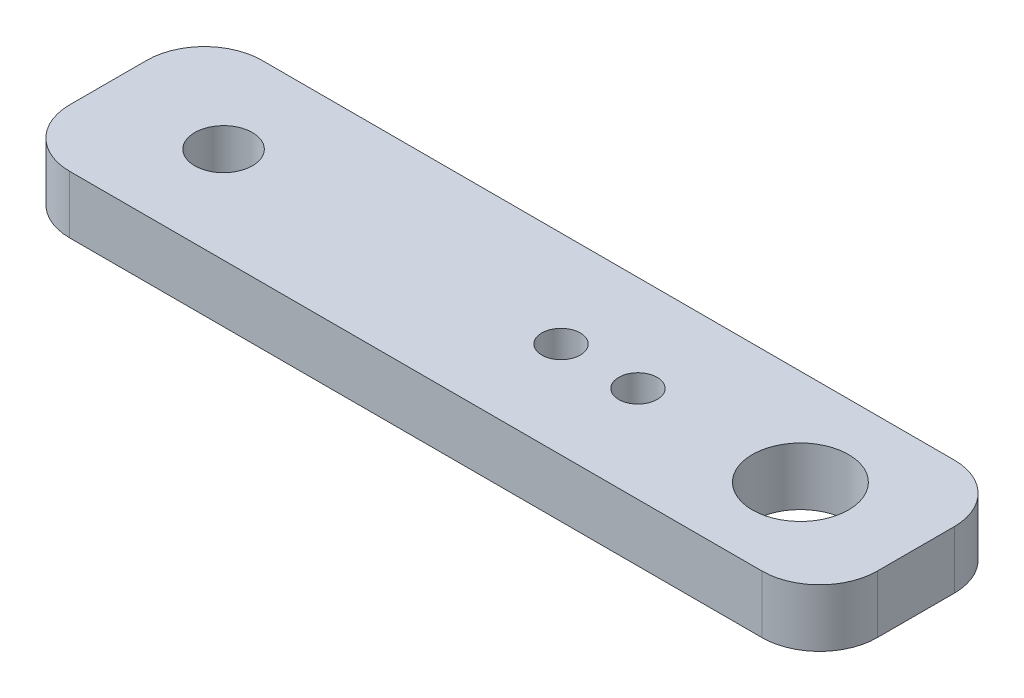
SolidWorks part; units mm, degrees
ref_plane "Front Plane" through (0, 0, 0) normal (0, 0, 1) x (1, 0, 0)
ref_plane "Top Plane" through (0, 0, 0) normal (0, 1, 0) x (1, 0, 0)
ref_plane "Right Plane" through (0, 0, 0) normal (1, 0, 0) x (0, 0, -1)
sketch "Sketch1" plane through (0, 0, 0) normal (0, 1, 0) x (1, 0, 0)
  line L1 (-21, 5) -> (21, 5)
  line L2 (-21, 5) -> (-21, -5)
  line L3 (-21, -5) -> (21, -5)
  line L4 (21, 5) -> (21, -5)
  line L5 (-21, 5) -> (21, -5) construction
  line L6 (-21, -5) -> (21, 5) construction
  point P0 (0, 0)
  dimension "D1" = 10
  dimension "D2" = 42
extrude "Boss-Extrude1" add sketch "Sketch1" along normal blind 3
hole_wizard "Ø5.0mm Dowel Hole1" positions "Sketch5" profile "Sketch6" hole size "Ø5.0" standard "ISO" end condition through all
sketch "Sketch5" plane through (0, 3, 0) normal (0, 1, 0) x (1, 0, 0)
  line L0 (21, -5) -> (21, 5) construction
  point P0 (15, 0)
  dimension "D1" = 6
sketch "Sketch6" plane through (15, 3, 0) normal (1, 0, 0) x (0, 0, 1)
  line L0 (0, 0) -> (0, 3)
  line L1 (0, 3) -> (2.5, 3)
  line L2 (2.5, 3) -> (2.5, 0)
  line L5 (2.5, 0) -> (0, 0)
  line L11 (0, -6.35) -> (0, 107.95) construction
  dimension "Thru Hole Dia." = 5
  dimension "Thru Hole Depth" = 3
hole_wizard "Ø3.0mm Dowel Hole1" positions "Sketch3" profile "Sketch4" hole size "Ø3.0" standard "ISO" end condition through all
sketch "Sketch3" plane through (0, 3, 0) normal (0, 1, 0) x (1, 0, 0)
  circle A4 centre (15, 0) radius 2.5 construction
  point P0 (-15, 0)
  dimension "D1" = 30
sketch "Sketch4" plane through (-15, 3, 0) normal (1, 0, 0) x (0, 0, 1)
  line L0 (0, 0) -> (0, 3)
  line L1 (0, 3) -> (1.5, 3)
  line L2 (1.5, 3) -> (1.5, 0)
  line L5 (1.5, 0) -> (0, 0)
  line L11 (0, -6.35) -> (0, 107.95) construction
  dimension "Thru Hole Dia." = 3
  dimension "Thru Hole Depth" = 3
sketch "Sketch2" plane through (0, 3, 0) normal (0, 1, 0) x (1, 0, 0)
  line L0 (15, 5) -> (15, -5) construction
  line L1 (-21, -5) -> (21, -5) construction
  line L3 (21, 0) -> (-21, 0) construction
  line L4 (21, -5) -> (21, 5) construction
  line L5 (-21, 5) -> (-21, -5) construction
  circle A3 centre (6.55, 0) radius 1
  circle A4 centre (2.55, 0) radius 1
  point P10 (15, 0)
  dimension "D1" = 2
  dimension "D2" = 8.45
  dimension "D3" = 4
extrude "Cut-Extrude1" cut sketch "Sketch2" against normal blind 3
fillet "Fillet1" radius 3 4 edges at (21, 1.5, 5) (21, 1.5, -5) (-21, 1.5, -5) (-21, 1.5, 5)
equation "\"globalength1\"=55"
